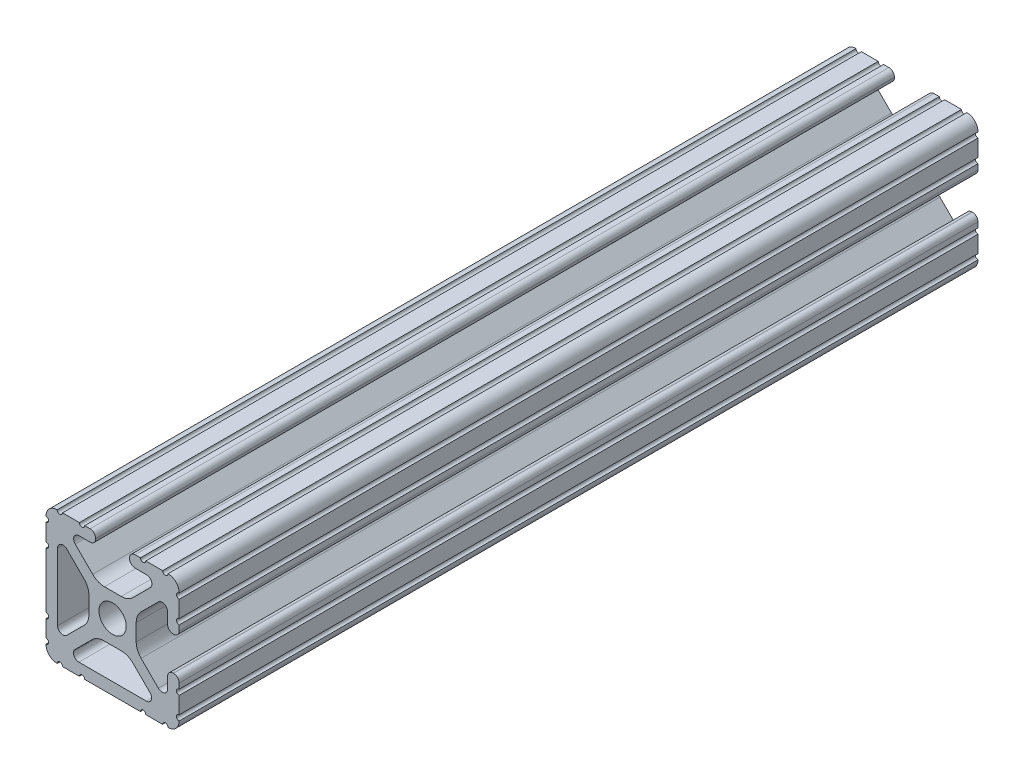
SolidWorks part; units mm, degrees
ref_plane "Front Plane" through (0, 0, 0) normal (0, 0, 1) x (1, 0, 0)
ref_plane "Top Plane" through (0, 0, 0) normal (0, 1, 0) x (1, 0, 0)
ref_plane "Right Plane" through (0, 0, 0) normal (1, 0, 0) x (0, 0, -1)
sketch "Sketch1" plane through (0, 0, 0) normal (0, 0, 1) x (1, 0, 0)
  line L0 (-3.2512, 12.7) -> (-3.2512, -12.7) construction
  line L1 (12.7, -12.7) -> (-12.7, -12.7)
  line L2 (12.7, -12.7) -> (12.7, 12.7)
  line L3 (12.7, 12.7) -> (-12.7, 12.7)
  line L4 (-12.7, -12.7) -> (-12.7, 12.7)
  line L5 (0, 12.7) -> (0, -12.7) construction
  line L6 (12.7, 0) -> (-12.7, 0) construction
  line L7 (-3.2512, -12.7) -> (3.2512, 12.7) construction
  line L8 (3.2512, 12.7) -> (3.2512, -12.7) construction
  circle A0 centre (0, 0) radius 2.6035
  point P0 (0, 0)
  line B0 (-10.4902, 6.4021) -> (-10.4902, -6.4254)
  line B1 (-5.4405, 3.8388) -> (-8.737, 7.1292)
  line B2 (-4.5085, -1.5917) -> (-4.5085, 1.5917)
  line B3 (-8.7534, -7.1457) -> (-5.4405, -3.8388)
  line B4 (-6.436, -10.4062) -> (6.4276, -10.4062)
  line B5 (-3.9003, -5.4237) -> (-7.1537, -8.6712)
  line B6 (1.6573, -4.4958) -> (-1.6573, -4.4958)
  line B7 (7.1478, -8.6653) -> (3.9003, -5.4237)
  line B8 (-5.3171, -12.7) -> (5.3171, -12.7)
  line B9 (6.3331, -12.7) -> (9.5504, -12.7)
  line B10 (12.7, -9.5504) -> (12.7, -6.3331)
  line B11 (12.7, -5.3171) -> (12.7, -4.2875)
  line B12 (11.651, -3.2385) -> (11.5392, -3.2385)
  line B13 (10.4902, -4.2875) -> (10.4902, -6.4021)
  line B14 (8.737, -7.1292) -> (5.4405, -3.8388)
  line B15 (4.5085, -1.5917) -> (4.5085, 1.5917)
  line B16 (5.4405, 3.8388) -> (8.737, 7.1292)
  line B17 (10.4902, 6.4021) -> (10.4902, 4.2875)
  line B18 (11.5392, 3.2385) -> (11.651, 3.2385)
  line B19 (12.7, 4.2875) -> (12.7, 5.3171)
  line B20 (12.7, 6.3331) -> (12.7, 9.5504)
  line B21 (9.5504, 12.7) -> (6.3331, 12.7)
  line B22 (5.3171, 12.7) -> (4.2875, 12.7)
  line B23 (3.2385, 11.651) -> (3.2385, 11.5392)
  line B24 (4.2875, 10.4902) -> (6.4768, 10.4902)
  line B25 (7.2072, 8.7246) -> (3.9003, 5.4237)
  line B26 (1.6573, 4.4958) -> (-1.5537, 4.4958)
  line B27 (-3.7967, 5.4237) -> (-7.1342, 8.7551)
  line B28 (-6.4164, 10.4902) -> (-4.2875, 10.4902)
  line B29 (-3.2385, 11.5392) -> (-3.2385, 11.651)
  line B30 (-4.2875, 12.7) -> (-5.3171, 12.7)
  line B31 (-6.3331, 12.7) -> (-9.5504, 12.7)
  line B32 (-12.7, 9.5504) -> (-12.7, 6.3331)
  line B33 (-12.7, 5.3171) -> (-12.7, -5.3171)
  line B34 (-12.7, -6.3331) -> (-12.7, -9.5504)
  line B35 (-9.5504, -12.7) -> (-6.3331, -12.7)
  circle B36 centre (0, 0) radius 2.6035
  arc B37 (-10.4902, -6.4254) -> (-8.7534, -7.1457) centre (-9.4724, -6.4254) ccw
  arc B38 (-8.737, 7.1292) -> (-10.4902, 6.4021) centre (-9.4628, 6.4021) ccw
  arc B39 (-4.5085, 1.5917) -> (-5.4405, 3.8388) centre (-7.6835, 1.5917) ccw
  arc B40 (-5.4405, -3.8388) -> (-4.5085, -1.5917) centre (-7.6835, -1.5917) ccw
  arc B41 (6.4276, -10.4062) -> (7.1478, -8.6653) centre (6.4276, -9.3868) ccw
  arc B42 (-7.1537, -8.6712) -> (-6.436, -10.4062) centre (-6.436, -9.3902) ccw
  arc B43 (-1.6573, -4.4958) -> (-3.9003, -5.4237) centre (-1.6573, -7.6708) ccw
  arc B44 (3.9003, -5.4237) -> (1.6573, -4.4958) centre (1.6573, -7.6708) ccw
  arc B45 (-5.3171, -12.7) -> (-6.3331, -12.7) centre (-5.8251, -12.7) ccw
  arc B46 (6.3331, -12.7) -> (5.3171, -12.7) centre (5.8251, -12.7) ccw
  arc B47 (10.5664, -12.6998) -> (9.5504, -12.7) centre (10.0584, -12.7) ccw
  arc B48 (10.5664, -12.6998) -> (12.6998, -10.5664) centre (10.5918, -10.5918) ccw
  arc B49 (12.7, -9.5504) -> (12.6998, -10.5664) centre (12.7, -10.0584) ccw
  arc B50 (12.7, -5.3171) -> (12.7, -6.3331) centre (12.7, -5.8251) ccw
  arc B51 (12.7, -4.2875) -> (11.651, -3.2385) centre (11.651, -4.2875) ccw
  arc B52 (11.5392, -3.2385) -> (10.4902, -4.2875) centre (11.5392, -4.2875) ccw
  arc B53 (8.737, -7.1292) -> (10.4902, -6.4021) centre (9.4628, -6.4021) ccw
  arc B54 (4.5085, -1.5917) -> (5.4405, -3.8388) centre (7.6835, -1.5917) ccw
  arc B55 (5.4405, 3.8388) -> (4.5085, 1.5917) centre (7.6835, 1.5917) ccw
  arc B56 (10.4902, 6.4021) -> (8.737, 7.1292) centre (9.4628, 6.4021) ccw
  arc B57 (10.4902, 4.2875) -> (11.5392, 3.2385) centre (11.5392, 4.2875) ccw
  arc B58 (11.651, 3.2385) -> (12.7, 4.2875) centre (11.651, 4.2875) ccw
  arc B59 (12.7, 6.3331) -> (12.7, 5.3171) centre (12.7, 5.8251) ccw
  arc B60 (12.6998, 10.5664) -> (12.7, 9.5504) centre (12.7, 10.0584) ccw
  arc B61 (12.6998, 10.5664) -> (10.5664, 12.6998) centre (10.5918, 10.5918) ccw
  arc B62 (9.5504, 12.7) -> (10.5664, 12.6998) centre (10.0584, 12.7) ccw
  arc B63 (5.3171, 12.7) -> (6.3331, 12.7) centre (5.8251, 12.7) ccw
  arc B64 (4.2875, 12.7) -> (3.2385, 11.651) centre (4.2875, 11.651) ccw
  arc B65 (3.2385, 11.5392) -> (4.2875, 10.4902) centre (4.2875, 11.5392) ccw
  arc B66 (7.2072, 8.7246) -> (6.4768, 10.4902) centre (6.4768, 9.4563) ccw
  arc B67 (1.6573, 4.4958) -> (3.9003, 5.4237) centre (1.6573, 7.6708) ccw
  arc B68 (-3.7967, 5.4237) -> (-1.5537, 4.4958) centre (-1.5537, 7.6708) ccw
  arc B69 (-6.4164, 10.4902) -> (-7.1342, 8.7551) centre (-6.4164, 9.4742) ccw
  arc B70 (-4.2875, 10.4902) -> (-3.2385, 11.5392) centre (-4.2875, 11.5392) ccw
  arc B71 (-3.2385, 11.651) -> (-4.2875, 12.7) centre (-4.2875, 11.651) ccw
  arc B72 (-6.3331, 12.7) -> (-5.3171, 12.7) centre (-5.8251, 12.7) ccw
  arc B73 (-10.5664, 12.6998) -> (-9.5504, 12.7) centre (-10.0584, 12.7) ccw
  arc B74 (-10.5664, 12.6998) -> (-12.6998, 10.5664) centre (-10.5918, 10.5918) ccw
  arc B75 (-12.7, 9.5504) -> (-12.6998, 10.5664) centre (-12.7, 10.0584) ccw
  arc B76 (-12.7, 5.3171) -> (-12.7, 6.3331) centre (-12.7, 5.8251) ccw
  arc B77 (-12.7, -6.3331) -> (-12.7, -5.3171) centre (-12.7, -5.8251) ccw
  arc B78 (-12.6998, -10.5664) -> (-12.7, -9.5504) centre (-12.7, -10.0584) ccw
  arc B79 (-12.6998, -10.5664) -> (-10.5664, -12.6998) centre (-10.5918, -10.5918) ccw
  arc B80 (-9.5504, -12.7) -> (-10.5664, -12.6998) centre (-10.0584, -12.7) ccw
  dimension "Center Hole Diameter" = 5.207
  dimension "Rail Width" = 25.4
  dimension "Rail Height" = 25.4
  dimension "T-Slot Width" = 6.5024
sketch_block_instance "Block1-1"
sketch_block "Block1"
sketch "Sketch2" plane through (0, 0, 0) normal (1, 0, 0) x (0, 0, -1)
  line L0 (-76.2, 0) -> (76.2, 0) construction
  line L1 (-76.2, 12.7) -> (-76.2, -12.7) construction
  line L2 (-76.2, -12.7) -> (76.2, -12.7) construction
  line L3 (76.2, -12.7) -> (76.2, 12.7) construction
  line L4 (-25.4, 0) -> (-25.4, 12.7) construction
  line L5 (-25.4, 12.7) -> (25.4, 12.7) construction
  line L6 (25.4, 12.7) -> (25.4, 0) construction
  line L7 (-3048, -12.7) -> (3048, -12.7)
  line L8 (-12.7, 12.7) -> (12.7, 12.7)
  point P7 (25.4, 0)
  point P11 (-25.4, 0)
  point P16 (0, -12.7)
  point P19 (0, 12.7)
  dimension "D1" = 50.8
  dimension "D2" = 50.8
  dimension "Rep Length" = 152.4
  dimension "Length Range [Max]" = 6096
  dimension "Length Range [Min]" = 25.4
sketch "Sketch3" plane through (0, 0, 0) normal (0, 0, 1) x (1, 0, 0)
  line L0 (6.3331, -12.7) -> (9.5504, -12.7) construction
  line L1 (12.7, -9.5504) -> (12.7, -6.3331) construction
  line L2 (12.7, -5.3171) -> (12.7, -4.2875) construction
  line L3 (11.651, -3.2385) -> (11.5392, -3.2385) construction
  line L12 (10.4902, -4.2875) -> (10.4902, -6.4021) construction
  line L13 (8.737, -7.1292) -> (5.4405, -3.8388) construction
  line L14 (4.5085, -1.5917) -> (4.5085, 1.5917) construction
  line L15 (5.4405, 3.8388) -> (8.737, 7.1292) construction
  line L16 (10.4902, 6.4021) -> (10.4902, 4.2875) construction
  line L17 (11.5392, 3.2385) -> (11.651, 3.2385) construction
  line L18 (12.7, 4.2875) -> (12.7, 5.3171) construction
  line L19 (12.7, 6.3331) -> (12.7, 9.5504) construction
  line L20 (9.5504, 12.7) -> (6.3331, 12.7) construction
  line L21 (5.3171, 12.7) -> (4.2875, 12.7) construction
  line L22 (3.2385, 11.651) -> (3.2385, 11.5392) construction
  line L23 (4.2875, 10.4902) -> (6.4768, 10.4902) construction
  line L24 (7.2072, 8.7246) -> (3.9003, 5.4237) construction
  line L25 (1.6573, 4.4958) -> (-1.5537, 4.4958) construction
  line L26 (-3.7967, 5.4237) -> (-7.1342, 8.7551) construction
  line L27 (-6.4164, 10.4902) -> (-4.2875, 10.4902) construction
  line L28 (-3.2385, 11.5392) -> (-3.2385, 11.651) construction
  line L29 (-4.2875, 12.7) -> (-5.3171, 12.7) construction
  line L30 (-6.3331, 12.7) -> (-9.5504, 12.7) construction
  line L31 (-12.7, 9.5504) -> (-12.7, 6.3331) construction
  line L32 (-12.7, 5.3171) -> (-12.7, -5.3171) construction
  line L33 (-12.7, -6.3331) -> (-12.7, -9.5504) construction
  line L34 (-9.5504, -12.7) -> (-6.3331, -12.7) construction
  line L35 (-5.3171, -12.7) -> (5.3171, -12.7) construction
  line L36 (-8.7534, -7.1457) -> (-5.4405, -3.8388) construction
  line L37 (-10.4902, 6.4021) -> (-10.4902, -6.4254) construction
  line L38 (-5.4405, 3.8388) -> (-8.737, 7.1292) construction
  line L39 (-4.5085, -1.5917) -> (-4.5085, 1.5917) construction
  line L40 (7.1478, -8.6653) -> (3.9003, -5.4237) construction
  line L41 (-6.436, -10.4062) -> (6.4276, -10.4062) construction
  line L42 (-3.9003, -5.4237) -> (-7.1537, -8.6712) construction
  line L43 (1.6573, -4.4958) -> (-1.6573, -4.4958) construction
  line L44 (6.3331, -12.7) -> (9.5504, -12.7)
  line L45 (12.7, -9.5504) -> (12.7, -6.3331)
  line L46 (12.7, -5.3171) -> (12.7, -4.2875)
  line L47 (11.651, -3.2385) -> (11.5392, -3.2385)
  line L48 (10.4902, -4.2875) -> (10.4902, -6.4021)
  line L49 (8.737, -7.1292) -> (5.4405, -3.8388)
  line L50 (4.5085, -1.5917) -> (4.5085, 1.5917)
  line L51 (5.4405, 3.8388) -> (8.737, 7.1292)
  line L52 (10.4902, 6.4021) -> (10.4902, 4.2875)
  line L53 (11.5392, 3.2385) -> (11.651, 3.2385)
  line L54 (12.7, 4.2875) -> (12.7, 5.3171)
  line L55 (12.7, 6.3331) -> (12.7, 9.5504)
  line L56 (9.5504, 12.7) -> (6.3331, 12.7)
  line L57 (5.3171, 12.7) -> (4.2875, 12.7)
  line L58 (3.2385, 11.651) -> (3.2385, 11.5392)
  line L59 (4.2875, 10.4902) -> (6.4768, 10.4902)
  line L60 (7.2072, 8.7246) -> (3.9003, 5.4237)
  line L61 (1.6573, 4.4958) -> (-1.5537, 4.4958)
  line L62 (-3.7967, 5.4237) -> (-7.1342, 8.7551)
  line L63 (-6.4164, 10.4902) -> (-4.2875, 10.4902)
  line L64 (-3.2385, 11.5392) -> (-3.2385, 11.651)
  line L65 (-4.2875, 12.7) -> (-5.3171, 12.7)
  line L66 (-6.3331, 12.7) -> (-9.5504, 12.7)
  line L67 (-12.7, 9.5504) -> (-12.7, 6.3331)
  line L68 (-12.7, 5.3171) -> (-12.7, -5.3171)
  line L69 (-12.7, -6.3331) -> (-12.7, -9.5504)
  line L70 (-9.5504, -12.7) -> (-6.3331, -12.7)
  line L71 (-5.3171, -12.7) -> (5.3171, -12.7)
  line L72 (-8.7534, -7.1457) -> (-5.4405, -3.8388)
  line L73 (-10.4902, 6.4021) -> (-10.4902, -6.4254)
  line L74 (-5.4405, 3.8388) -> (-8.737, 7.1292)
  line L75 (-4.5085, -1.5917) -> (-4.5085, 1.5917)
  line L76 (7.1478, -8.6653) -> (3.9003, -5.4237)
  line L77 (-6.436, -10.4062) -> (6.4276, -10.4062)
  line L78 (-3.9003, -5.4237) -> (-7.1537, -8.6712)
  line L79 (1.6573, -4.4958) -> (-1.6573, -4.4958)
  arc A0 (10.5664, -12.6998) -> (9.5504, -12.7) centre (10.0584, -12.7) ccw construction
  circle A1 centre (0, 0) radius 2.6035
  circle A2 centre (0, 0) radius 2.6035
  arc A3 (10.5664, -12.6998) -> (12.6998, -10.5664) centre (10.5918, -10.5918) ccw construction
  arc A4 (12.7, -9.5504) -> (12.6998, -10.5664) centre (12.7, -10.0584) ccw construction
  arc A5 (12.7, -5.3171) -> (12.7, -6.3331) centre (12.7, -5.8251) ccw construction
  arc A6 (12.7, -4.2875) -> (11.651, -3.2385) centre (11.651, -4.2875) ccw construction
  arc A7 (11.5392, -3.2385) -> (10.4902, -4.2875) centre (11.5392, -4.2875) ccw construction
  arc A8 (8.737, -7.1292) -> (10.4902, -6.4021) centre (9.4628, -6.4021) ccw construction
  arc A9 (4.5085, -1.5917) -> (5.4405, -3.8388) centre (7.6835, -1.5917) ccw construction
  arc A10 (5.4405, 3.8388) -> (4.5085, 1.5917) centre (7.6835, 1.5917) ccw construction
  arc A11 (10.4902, 6.4021) -> (8.737, 7.1292) centre (9.4628, 6.4021) ccw construction
  arc A12 (10.4902, 4.2875) -> (11.5392, 3.2385) centre (11.5392, 4.2875) ccw construction
  arc A13 (11.651, 3.2385) -> (12.7, 4.2875) centre (11.651, 4.2875) ccw construction
  arc A14 (12.7, 6.3331) -> (12.7, 5.3171) centre (12.7, 5.8251) ccw construction
  arc A15 (12.6998, 10.5664) -> (12.7, 9.5504) centre (12.7, 10.0584) ccw construction
  arc A16 (12.6998, 10.5664) -> (10.5664, 12.6998) centre (10.5918, 10.5918) ccw construction
  arc A17 (9.5504, 12.7) -> (10.5664, 12.6998) centre (10.0584, 12.7) ccw construction
  arc A18 (5.3171, 12.7) -> (6.3331, 12.7) centre (5.8251, 12.7) ccw construction
  arc A19 (4.2875, 12.7) -> (3.2385, 11.651) centre (4.2875, 11.651) ccw construction
  arc A20 (3.2385, 11.5392) -> (4.2875, 10.4902) centre (4.2875, 11.5392) ccw construction
  arc A21 (7.2072, 8.7246) -> (6.4768, 10.4902) centre (6.4768, 9.4563) ccw construction
  arc A22 (1.6573, 4.4958) -> (3.9003, 5.4237) centre (1.6573, 7.6708) ccw construction
  arc A23 (-3.7967, 5.4237) -> (-1.5537, 4.4958) centre (-1.5537, 7.6708) ccw construction
  arc A24 (-6.4164, 10.4902) -> (-7.1342, 8.7551) centre (-6.4164, 9.4742) ccw construction
  arc A25 (-4.2875, 10.4902) -> (-3.2385, 11.5392) centre (-4.2875, 11.5392) ccw construction
  arc A26 (-3.2385, 11.651) -> (-4.2875, 12.7) centre (-4.2875, 11.651) ccw construction
  arc A27 (-6.3331, 12.7) -> (-5.3171, 12.7) centre (-5.8251, 12.7) ccw construction
  arc A28 (-10.5664, 12.6998) -> (-9.5504, 12.7) centre (-10.0584, 12.7) ccw construction
  arc A29 (-10.5664, 12.6998) -> (-12.6998, 10.5664) centre (-10.5918, 10.5918) ccw construction
  arc A30 (-12.7, 9.5504) -> (-12.6998, 10.5664) centre (-12.7, 10.0584) ccw construction
  arc A31 (-12.7, 5.3171) -> (-12.7, 6.3331) centre (-12.7, 5.8251) ccw construction
  arc A32 (-12.7, -6.3331) -> (-12.7, -5.3171) centre (-12.7, -5.8251) ccw construction
  arc A33 (-12.6998, -10.5664) -> (-12.7, -9.5504) centre (-12.7, -10.0584) ccw construction
  arc A34 (-12.6998, -10.5664) -> (-10.5664, -12.6998) centre (-10.5918, -10.5918) ccw construction
  arc A35 (-9.5504, -12.7) -> (-10.5664, -12.6998) centre (-10.0584, -12.7) ccw construction
  arc A36 (-5.3171, -12.7) -> (-6.3331, -12.7) centre (-5.8251, -12.7) ccw construction
  arc A37 (6.3331, -12.7) -> (5.3171, -12.7) centre (5.8251, -12.7) ccw construction
  arc A38 (-10.4902, -6.4254) -> (-8.7534, -7.1457) centre (-9.4724, -6.4254) ccw construction
  arc A39 (-8.737, 7.1292) -> (-10.4902, 6.4021) centre (-9.4628, 6.4021) ccw construction
  arc A40 (-4.5085, 1.5917) -> (-5.4405, 3.8388) centre (-7.6835, 1.5917) ccw construction
  arc A41 (-5.4405, -3.8388) -> (-4.5085, -1.5917) centre (-7.6835, -1.5917) ccw construction
  circle A42 centre (0, 0) radius 2.6035 construction
  arc A43 (6.4276, -10.4062) -> (7.1478, -8.6653) centre (6.4276, -9.3868) ccw construction
  arc A44 (-7.1537, -8.6712) -> (-6.436, -10.4062) centre (-6.436, -9.3902) ccw construction
  arc A45 (-1.6573, -4.4958) -> (-3.9003, -5.4237) centre (-1.6573, -7.6708) ccw construction
  arc A46 (3.9003, -5.4237) -> (1.6573, -4.4958) centre (1.6573, -7.6708) ccw construction
  arc A47 (10.5664, -12.6998) -> (9.5504, -12.7) centre (10.0584, -12.7) ccw
  arc A48 (10.5664, -12.6998) -> (12.6998, -10.5664) centre (10.5918, -10.5918) ccw
  arc A49 (12.7, -9.5504) -> (12.6998, -10.5664) centre (12.7, -10.0584) ccw
  arc A50 (12.7, -5.3171) -> (12.7, -6.3331) centre (12.7, -5.8251) ccw
  arc A51 (12.7, -4.2875) -> (11.651, -3.2385) centre (11.651, -4.2875) ccw
  arc A52 (11.5392, -3.2385) -> (10.4902, -4.2875) centre (11.5392, -4.2875) ccw
  arc A53 (8.737, -7.1292) -> (10.4902, -6.4021) centre (9.4628, -6.4021) ccw
  arc A54 (4.5085, -1.5917) -> (5.4405, -3.8388) centre (7.6835, -1.5917) ccw
  arc A55 (5.4405, 3.8388) -> (4.5085, 1.5917) centre (7.6835, 1.5917) ccw
  arc A56 (10.4902, 6.4021) -> (8.737, 7.1292) centre (9.4628, 6.4021) ccw
  arc A57 (10.4902, 4.2875) -> (11.5392, 3.2385) centre (11.5392, 4.2875) ccw
  arc A58 (11.651, 3.2385) -> (12.7, 4.2875) centre (11.651, 4.2875) ccw
  arc A59 (12.7, 6.3331) -> (12.7, 5.3171) centre (12.7, 5.8251) ccw
  arc A60 (12.6998, 10.5664) -> (12.7, 9.5504) centre (12.7, 10.0584) ccw
  arc A61 (12.6998, 10.5664) -> (10.5664, 12.6998) centre (10.5918, 10.5918) ccw
  arc A62 (9.5504, 12.7) -> (10.5664, 12.6998) centre (10.0584, 12.7) ccw
  arc A63 (5.3171, 12.7) -> (6.3331, 12.7) centre (5.8251, 12.7) ccw
  arc A64 (4.2875, 12.7) -> (3.2385, 11.651) centre (4.2875, 11.651) ccw
  arc A65 (3.2385, 11.5392) -> (4.2875, 10.4902) centre (4.2875, 11.5392) ccw
  arc A66 (7.2072, 8.7246) -> (6.4768, 10.4902) centre (6.4768, 9.4563) ccw
  arc A67 (1.6573, 4.4958) -> (3.9003, 5.4237) centre (1.6573, 7.6708) ccw
  arc A68 (-3.7967, 5.4237) -> (-1.5537, 4.4958) centre (-1.5537, 7.6708) ccw
  arc A69 (-6.4164, 10.4902) -> (-7.1342, 8.7551) centre (-6.4164, 9.4742) ccw
  arc A70 (-4.2875, 10.4902) -> (-3.2385, 11.5392) centre (-4.2875, 11.5392) ccw
  arc A71 (-3.2385, 11.651) -> (-4.2875, 12.7) centre (-4.2875, 11.651) ccw
  arc A72 (-6.3331, 12.7) -> (-5.3171, 12.7) centre (-5.8251, 12.7) ccw
  arc A73 (-10.5664, 12.6998) -> (-9.5504, 12.7) centre (-10.0584, 12.7) ccw
  arc A74 (-10.5664, 12.6998) -> (-12.6998, 10.5664) centre (-10.5918, 10.5918) ccw
  arc A75 (-12.7, 9.5504) -> (-12.6998, 10.5664) centre (-12.7, 10.0584) ccw
  arc A76 (-12.7, 5.3171) -> (-12.7, 6.3331) centre (-12.7, 5.8251) ccw
  arc A77 (-12.7, -6.3331) -> (-12.7, -5.3171) centre (-12.7, -5.8251) ccw
  arc A78 (-12.6998, -10.5664) -> (-12.7, -9.5504) centre (-12.7, -10.0584) ccw
  arc A79 (-12.6998, -10.5664) -> (-10.5664, -12.6998) centre (-10.5918, -10.5918) ccw
  arc A80 (-9.5504, -12.7) -> (-10.5664, -12.6998) centre (-10.0584, -12.7) ccw
  arc A81 (-5.3171, -12.7) -> (-6.3331, -12.7) centre (-5.8251, -12.7) ccw
  arc A82 (6.3331, -12.7) -> (5.3171, -12.7) centre (5.8251, -12.7) ccw
  arc A83 (-10.4902, -6.4254) -> (-8.7534, -7.1457) centre (-9.4724, -6.4254) ccw
  arc A84 (-8.737, 7.1292) -> (-10.4902, 6.4021) centre (-9.4628, 6.4021) ccw
  arc A85 (-4.5085, 1.5917) -> (-5.4405, 3.8388) centre (-7.6835, 1.5917) ccw
  arc A86 (-5.4405, -3.8388) -> (-4.5085, -1.5917) centre (-7.6835, -1.5917) ccw
  circle A87 centre (0, 0) radius 2.6035
  arc A88 (6.4276, -10.4062) -> (7.1478, -8.6653) centre (6.4276, -9.3868) ccw
  arc A89 (-7.1537, -8.6712) -> (-6.436, -10.4062) centre (-6.436, -9.3902) ccw
  arc A90 (-1.6573, -4.4958) -> (-3.9003, -5.4237) centre (-1.6573, -7.6708) ccw
  arc A91 (3.9003, -5.4237) -> (1.6573, -4.4958) centre (1.6573, -7.6708) ccw
  dimension "D1" = 0
extrude "Boss-Extrude1" add sketch "Sketch3" along normal up to vertex (76.2 mm away) and the other way up to vertex (76.2 mm away) contours A82 L44 A47 A48 A49 L45 A50 L46 A51 L47 A52 L48 A53 L49 A54 L50 A55 L51 A56 L52 A57 L53 A58 L54 A59 L55 A60 A61 A62 L56 A63 L57 A64 L58 A65 L59 A66 L60 A67 L61 A68 L62 A69 L63 A70 L64 A71 L65 A72 L66 A73 up to point (0, 0, 76.2) other way up to point (0, 0, -76.2)
